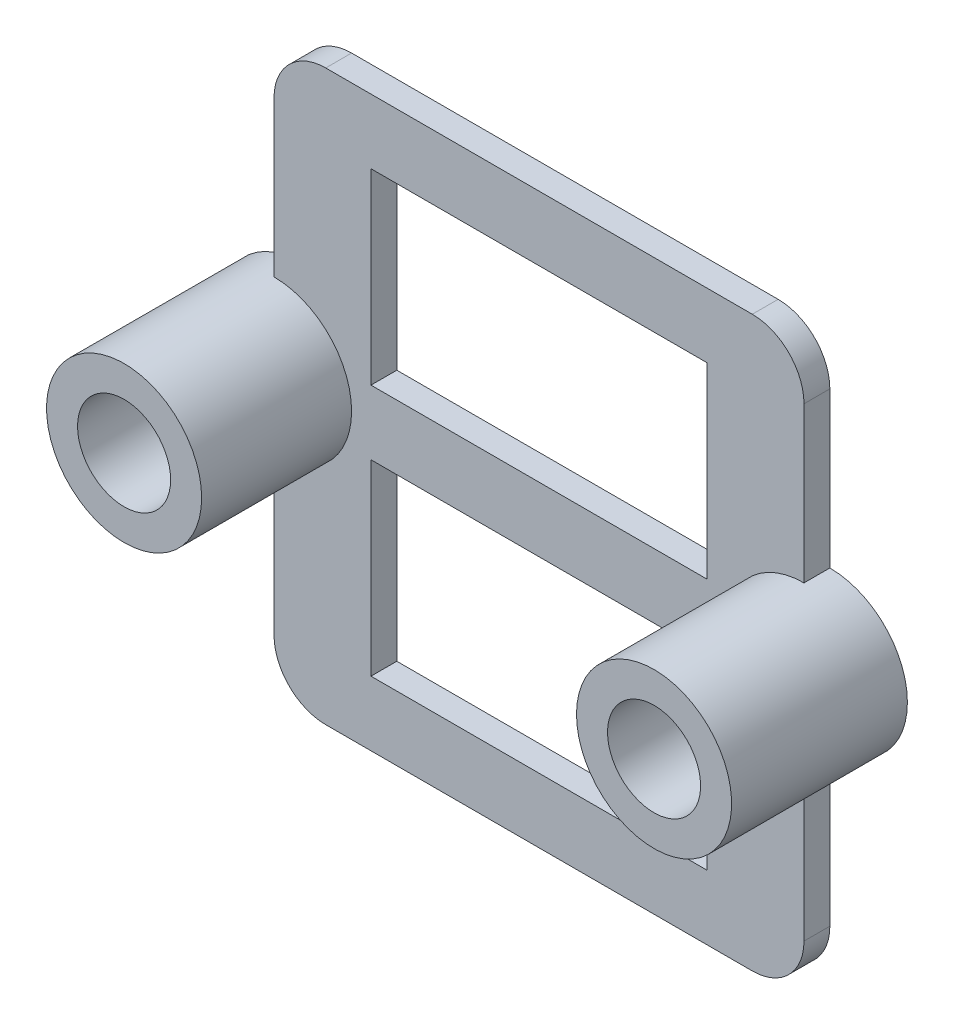
SolidWorks part; units mm, degrees
ref_plane "Front Plane" through (0, 0, 0) normal (0, 0, 1) x (1, 0, 0)
ref_plane "Top Plane" through (0, 0, 0) normal (0, 1, 0) x (1, 0, 0)
ref_plane "Right Plane" through (0, 0, 0) normal (1, 0, 0) x (0, 0, -1)
sketch "Sketch1" plane through (0, 0, 0) normal (0, 0, 1) x (1, 0, 0)
  line L0 (6.5, -8.5) -> (-6.5, -8.5)
  line L1 (6.5, 8.5) -> (-6.5, 8.5)
  line L2 (-6.5, 11) -> (6.5, 11)
  line L3 (-6.5, 1.25) -> (-6.5, 8.5)
  line L4 (-6.5, -1.25) -> (-6.5, -8.5)
  line L5 (-6.5, 11) -> (-10.25, 11)
  line L6 (-10.25, 11) -> (-10.25, 3)
  line L7 (-10.25, -3) -> (-10.25, -11)
  line L8 (-10.25, -11) -> (-6.5, -11)
  line L10 (-6.5, -11) -> (6.5, -11)
  line L11 (10.25, -11) -> (6.5, -11)
  line L12 (10.25, -3) -> (10.25, -11)
  line L13 (10.25, 11) -> (10.25, 3)
  line L14 (-6.5, 1.25) -> (6.5, 1.25)
  line L15 (6.5, 11) -> (10.25, 11)
  line L16 (6.5, -1.25) -> (-6.5, -1.25)
  line L17 (6.5, -1.25) -> (6.5, -8.5)
  line L18 (6.5, 1.25) -> (6.5, 8.5)
  arc A0 (10.25, 3) -> (10.25, -3) centre (10.25, 0) cw
  circle A1 centre (-10.25, 0) radius 1.8
  arc A2 (-10.25, 3) -> (-10.25, -3) centre (-10.25, 0) ccw
  circle A3 centre (10.25, 0) radius 1.8
  point P1 (0, 8.5)
  point P7 (0, -8.5)
  point P28 (0, -1.25)
  point P29 (0, 1.25)
  point P30 (0, -11)
  point P35 (0, 11)
  dimension "D1" = 3.6
  dimension "D3" = 3
  dimension "D7" = 3.6
  dimension "D2" = 3.75
  dimension "D4" = 2.5
  dimension "D5" = 2.5
  dimension "D6" = 2.5
extrude "Boss-Extrude1" add sketch "Sketch1" along normal blind 1
ref_plane "Plane1" through (0, 0, 1) normal (0, 0, 1) x (1, 0, 0)
sketch "Sketch2" plane through (0, 0, 1) normal (0, 0, 1) x (1, 0, 0)
  circle A0 centre (-10.25, 0) radius 1.8
  circle A1 centre (-10.25, 0) radius 3
  circle A2 centre (10.25, 0) radius 3
  circle A3 centre (10.25, 0) radius 1.8
  point P0 (-10.25, 0)
  dimension "D1" = 3.6
  dimension "D2" = 3.6
extrude "Boss-Extrude2" add sketch "Sketch2" along normal blind 5.8
fillet "Fillet4" radius 2 1 edges at (-10.25, 11, 0.5)
fillet "Fillet5" radius 2 1 edges at (10.25, 11, 0.5)
fillet "Fillet6" radius 2 1 edges at (-10.25, -11, 0.5)
fillet "Fillet7" radius 2 1 edges at (10.25, -11, 0.5)
